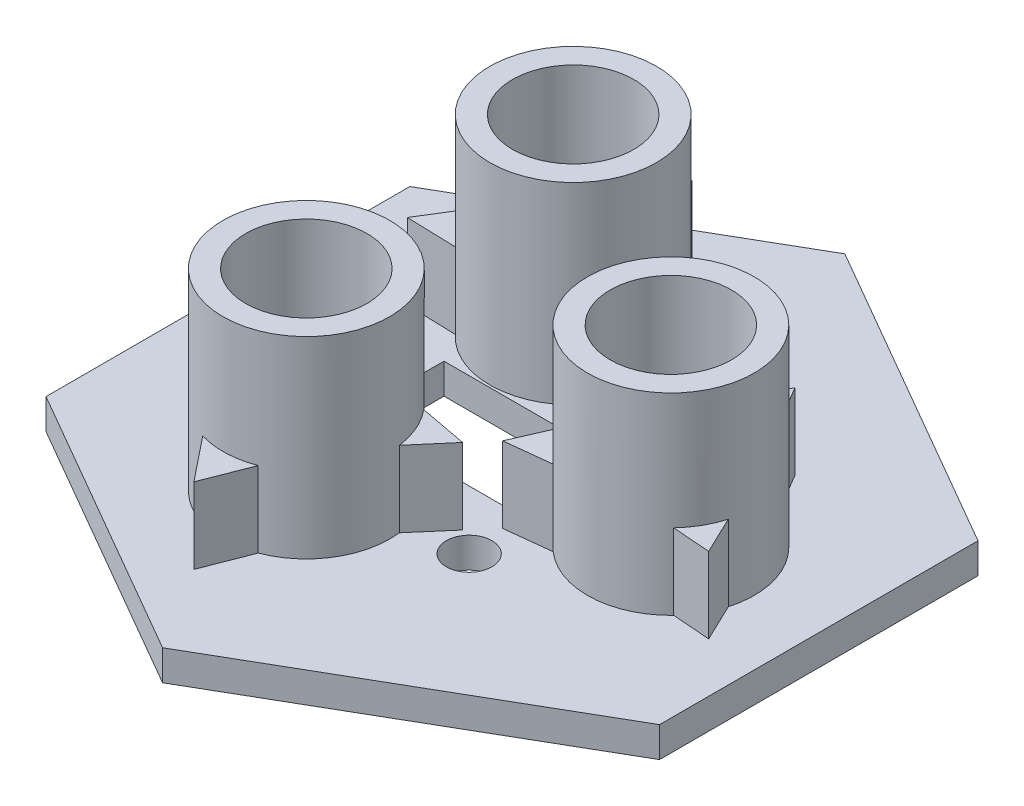
SolidWorks part; units mm, degrees
ref_plane "Front Plane" through (0, 0, 0) normal (0, 0, 1) x (1, 0, 0)
ref_plane "Top Plane" through (0, 0, 0) normal (0, 1, 0) x (1, 0, 0)
ref_plane "Right Plane" through (0, 0, 0) normal (1, 0, 0) x (0, 0, -1)
sketch "Sketch1" plane through (0, 0, 0) normal (0, 1, 0) x (1, 0, 0)
  line L1 (76.2, 0) -> (-38.1, 65.9911)
  line L2 (-38.1, 65.9911) -> (-38.1, -65.9911)
  line L3 (-38.1, -65.9911) -> (76.2, 0)
  circle A0 centre (0, 0) radius 38.1 construction
  dimension "D1" = 76.2
extrude "Boss-Extrude1" add sketch "Sketch1" along normal blind 4
sketch "Sketch2" plane through (0, 4, 0) normal (0, 1, 0) x (1, 0, 0)
  line L0 (0, 0) -> (20.32, 0) construction
  line L1 (0, 0) -> (-10.16, 17.5976) construction
  line L2 (0, 0) -> (-10.16, -17.5976) construction
  circle A0 centre (20.32, 0) radius 11
  circle A1 centre (-10.16, 17.5976) radius 11
  circle A2 centre (-10.16, -17.5976) radius 11
  dimension "D2" = 22
  dimension "D1" = 20.32
extrude "Boss-Extrude2" add sketch "Sketch2" along normal blind 25.4
sketch "Sketch3" plane through (0, 29.4, 0) normal (0, 1, 0) x (1, 0, 0)
  line L0 (-10.16, 6.5976) -> (-10.16, 28.5976) construction
  line L1 (20.32, -11) -> (20.32, 11) construction
  line L2 (-10.16, -28.5976) -> (-10.16, -6.5976) construction
  circle A0 centre (-10.16, 17.5976) radius 11 construction
  circle A1 centre (-10.16, 17.5976) radius 11 construction
  circle A2 centre (20.32, 0) radius 11 construction
  circle A3 centre (20.32, 0) radius 11 construction
  circle A4 centre (-10.16, -17.5976) radius 11 construction
  circle A5 centre (-10.16, -17.5976) radius 11 construction
  circle A6 centre (-10.16, 17.5976) radius 8
  circle A7 centre (20.32, 0) radius 8
  circle A8 centre (-10.16, -17.5976) radius 8
  dimension "D1" = 16
extrude "Cut-Extrude1" cut sketch "Sketch3" against normal blind 22.86
sketch "Sketch4" plane through (0, 4, 0) normal (0, 1, 0) x (1, 0, 0)
  line L0 (-38.1, 65.9911) -> (-1.7269, 44.9911)
  line L1 (76.2, 0) -> (-38.1, 65.9911) construction
  line L2 (-38.1, 65.9911) -> (-38.1, 23.9911)
  line L3 (-38.1, 65.9911) -> (-38.1, -65.9911) construction
  line L4 (-38.1, 23.9911) -> (-1.7269, 44.9911)
  line L5 (-38.1, -65.9911) -> (-1.7269, -44.9911)
  line L6 (-38.1, -65.9911) -> (76.2, 0) construction
  line L7 (-38.1, -65.9911) -> (-38.1, -23.9911)
  line L8 (76.2, 0) -> (39.8269, -21)
  line L9 (76.2, 0) -> (39.8269, 21)
  line L10 (-38.1, -23.9911) -> (-1.7269, -44.9911)
  line L11 (39.8269, 21) -> (39.8269, -21)
  dimension "D1" = 42
extrude "Cut-Extrude2" cut sketch "Sketch4" against normal blind 22.86
sketch "Sketch5" plane through (0, 0, 0) normal (0, -1, 0) x (-1, 0, 0)
  line L0 (38.1, 23.9911) -> (38.1, -23.9911) construction
  line L1 (15.9, -6.3) -> (-6.9, -6.3)
  line L2 (15.9, -6.3) -> (15.9, 6.3)
  line L3 (15.9, 6.3) -> (-6.9, 6.3)
  line L4 (-6.9, -6.3) -> (-6.9, 6.3)
  line L5 (15.9, -6.3) -> (-6.9, 6.3) construction
  line L6 (15.9, 6.3) -> (-6.9, -6.3) construction
  circle A0 centre (-7.7531, -14.0369) radius 3
  point P0 (0, 0)
  dimension "D4" = 6
  dimension "D1" = 12.6
  dimension "D2" = 22.8
  dimension "D3" = 22.2
extrude "Cut-Extrude3" cut sketch "Sketch5" against normal blind 4
sketch "Sketch6" plane through (0, 4, 0) normal (0, 1, 0) x (1, 0, 0)
  line L0 (-18.16, 17.5976) -> (13.4106, 17.5976) construction
  line L14 (-6.0613, 26.2731) -> (-10.1962, 33.3095)
  line L15 (-10.1962, 33.3095) -> (-14.2225, 26.2104)
  line L16 (-14.2225, 26.2104) -> (-6.0613, 26.2731)
  line L17 (-15.5534, 10.0194) -> (-19.9027, 18.0977)
  line L18 (-19.9027, 18.0977) -> (-24.7241, 10.2919)
  line L19 (-24.7241, 10.2919) -> (-15.5534, 10.0194)
  line L20 (4.6661, 11.8398) -> (-0.0289, 18.9879)
  line L21 (-0.0289, 18.9879) -> (-3.8718, 11.3479)
  line L22 (-3.8718, 11.3479) -> (4.6661, 11.8398)
  line L23 (25.0156, 8.329) -> (20.2853, 16.402)
  line L24 (20.2853, 16.402) -> (15.6591, 8.2689)
  line L25 (15.6591, 8.2689) -> (25.0156, 8.329)
  line L26 (33.2763, -7.9732) -> (30.1219, -1.3794)
  line L27 (30.1219, -1.3794) -> (25.9887, -7.408)
  line L28 (25.9887, -7.408) -> (33.2763, -7.9732)
  line L29 (15.6591, -7.9732) -> (10.5271, -1.0114)
  line L30 (10.5271, -1.0114) -> (7.064, -8.9366)
  line L31 (7.064, -8.9366) -> (15.6591, -7.9732)
  line L32 (-15.5534, -9.9637) -> (-23.6451, -9.6112)
  line L33 (-23.6451, -9.6112) -> (-19.9046, -16.795)
  line L34 (-19.9046, -16.795) -> (-15.5534, -9.9637)
  line L35 (-5.1702, -25.1584) -> (-14.524, -26.5886)
  line L36 (-14.524, -26.5886) -> (-8.6085, -33.9741)
  line L37 (-8.6085, -33.9741) -> (-5.1702, -25.1584)
  line L38 (-0.9012, -18.1892) -> (4.6141, -11.7583)
  line L39 (4.6141, -11.7583) -> (-3.7129, -10.1974)
  line L40 (-3.7129, -10.1974) -> (-0.9012, -18.1892)
  circle A0 centre (-10.16, 17.5976) radius 8 construction
  circle A1 centre (-10.16, 17.5976) radius 8 construction
  circle A2 centre (-10.16, 28.5976) radius 2.356 construction
  circle A3 centre (-10.16, 17.5976) radius 11 construction
  circle A4 centre (-10.16, 17.5976) radius 11 construction
  circle A5 centre (-20.0601, 12.803) radius 2.6485 construction
  circle A6 centre (0.2551, 14.0585) radius 2.4688 construction
  circle A7 centre (20.32, 11) radius 2.7011 construction
  circle A8 centre (20.32, 0) radius 11 construction
  circle A9 centre (20.32, 0) radius 11 construction
  circle A10 centre (29.7956, -5.5869) radius 2.1101 construction
  circle A11 centre (11.0834, -5.9737) radius 2.4967 construction
  circle A12 centre (-19.7011, -12.1233) radius 2.3381 construction
  circle A13 centre (-10.16, -17.5976) radius 11 construction
  circle A14 centre (-9.4342, -28.5737) radius 2.7316 construction
  circle A15 centre (-10.16, -17.5976) radius 11 construction
  circle A16 centre (0, -13.3817) radius 2.4457 construction
extrude "Boss-Extrude3" add sketch "Sketch6" along normal blind 10
sketch "Sketch7" plane through (0, 4, 0) normal (0, 1, 0) x (1, 0, 0)
  line L0 (6.9, 6.3) -> (6.9, -6.3) construction
  line L1 (4.48, 3.0282) -> (9.32, 3.0282)
  line L2 (4.48, 3.0282) -> (4.48, -3.0282)
  line L3 (4.48, -3.0282) -> (9.32, -3.0282)
  line L4 (9.32, 3.0282) -> (9.32, -3.0282)
  line L5 (4.48, 3.0282) -> (9.32, -3.0282) construction
  line L6 (4.48, -3.0282) -> (9.32, 3.0282) construction
  point P0 (6.9, 0)
extrude "Cut-Extrude4" cut sketch "Sketch7" against normal blind 10
